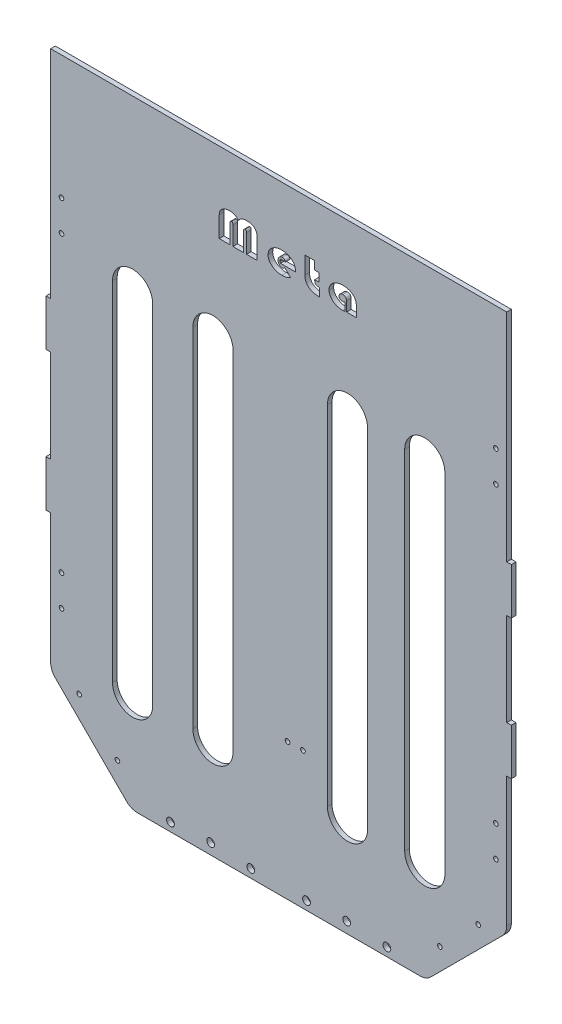
SolidWorks part; units mm, degrees
ref_plane "前视基准面" through (0, 0, 0) normal (0, 0, 1) x (1, 0, 0)
ref_plane "上视基准面" through (0, 0, 0) normal (0, 1, 0) x (1, 0, 0)
ref_plane "右视基准面" through (0, 0, 0) normal (1, 0, 0) x (0, 0, -1)
sketch "草图1" plane through (0, 0, 0) normal (0, 0, 1) x (1, 0, 0)
  line L0 (-147.5, 90) -> (-150.5, 90)
  line L1 (-147.5, 170) -> (147.5, 170)
  line L2 (-147.5, 170) -> (-147.5, 90)
  line L3 (-147.5, -170) -> (147.5, -170)
  line L4 (147.5, 170) -> (147.5, 90)
  line L5 (-147.5, 170) -> (147.5, -170) construction
  line L6 (-147.5, -170) -> (147.5, 170) construction
  line L7 (-150.5, 90) -> (-150.5, 60)
  line L8 (-150.5, 60) -> (-147.5, 60)
  line L9 (-147.5, 60) -> (-147.5, 0)
  line L10 (-147.5, 0) -> (-150.5, 0)
  line L11 (-150.5, 0) -> (-150.5, -30)
  line L12 (-150.5, -30) -> (-147.5, -30)
  line L13 (-147.5, -90) -> (-150.5, -90) construction
  line L14 (-150.5, -90) -> (-150.5, -120) construction
  line L15 (-150.5, -120) -> (-147.5, -120) construction
  line L16 (-147.5, -30) -> (-147.5, -90)
  line L17 (-147.5, -120) -> (-147.5, -170)
  line L18 (0, 0) -> (0, 121.9272) construction
  line L19 (147.5, -90) -> (150.5, -90) construction
  line L20 (150.5, -90) -> (150.5, -120) construction
  line L21 (150.5, -120) -> (147.5, -120) construction
  line L22 (147.5, 0) -> (150.5, 0)
  line L23 (150.5, 0) -> (150.5, -30)
  line L24 (150.5, -30) -> (147.5, -30)
  line L25 (147.5, 90) -> (150.5, 90)
  line L26 (150.5, 90) -> (150.5, 60)
  line L27 (150.5, 60) -> (147.5, 60)
  line L28 (147.5, -120) -> (147.5, -170)
  line L29 (147.5, -30) -> (147.5, -90)
  line L30 (147.5, 60) -> (147.5, 0)
  line L31 (-147.5, -90) -> (-147.5, -120)
  line L32 (147.5, -90) -> (147.5, -120)
  point P0 (0, 0)
  dimension "D1" = 295
  dimension "D2" = 340
  dimension "D3" = 30
  dimension "D4" = 3
  dimension "D5" = 80
  dimension "D6" = 3
  dimension "D7" = 30
  dimension "D8" = 30
  dimension "D9" = 3
  dimension "D10" = 50
  dimension "D11" = 60
extrude "凸台-拉伸1" add sketch "草图1" along normal blind 3
sketch "草图3" plane through (0, 0, 3) normal (0, 0, 1) x (1, 0, 0)
  line L0 (-147.5, -118) -> (-95.5, -170)
  line L1 (-147.5, -30) -> (-147.5, -170) construction
  line L2 (-147.5, -170) -> (147.5, -170) construction
  line L3 (-95.5, -170) -> (-147.5, -170)
  line L4 (-147.5, -170) -> (-147.5, -118)
  line L5 (147.5, -170) -> (147.5, -118)
  line L6 (147.5, -170) -> (147.5, -30) construction
  line L7 (147.5, -118) -> (95.5, -170)
  line L8 (95.5, -170) -> (147.5, -170)
  dimension "D1" = 52
  dimension "D2" = 52
  dimension "D3" = 52
  dimension "D4" = 52
extrude "切除-拉伸2" cut sketch "草图3" against normal through all
fillet "圆角1" [suppressed] radius 5
sketch "草图4" plane through (0, 0, 3) normal (0, 0, 1) x (1, 0, 0)
  line L0 (147.5, 170) -> (-147.5, 170) construction
  line L1 (147.5, 90) -> (147.5, 170) construction
  line L2 (147.5, -118) -> (147.5, -30) construction
  line L3 (0, 170) -> (0, 113.7599) construction
  circle A0 centre (140.5, 150) radius 1.5
  circle A1 centre (140.5, 130) radius 1.5
  circle A2 centre (140.5, -60) radius 1.5
  circle A3 centre (140.5, -80) radius 1.5
  circle A4 centre (-140.5, -80) radius 1.5
  circle A5 centre (-140.5, -60) radius 1.5
  circle A6 centre (-140.5, 130) radius 1.5
  circle A7 centre (-140.5, 150) radius 1.5
  dimension "D1" = 20
  dimension "D2" = 20
  dimension "D3" = 190
  dimension "D4" = 20
  dimension "D5" = 7
  dimension "D6" = 7
  dimension "D7" = 7
  dimension "D8" = 7
  dimension "D9" = 3
  dimension "D10" = 3
  dimension "D11" = 3
  dimension "D12" = 3
extrude "切除-拉伸3" cut sketch "草图4" against normal through all
sketch "草图5" plane through (0, 0, 3) normal (0, 0, 1) x (1, 0, 0)
  line L0 (-94.5, 120) -> (-94.5, -105) construction
  line L1 (-81.5, 120) -> (-81.5, -105)
  line L2 (-107.5, 120) -> (-107.5, -105)
  line L3 (147.5, 170) -> (-147.5, 170) construction
  line L4 (-147.5, 60) -> (-147.5, 0) construction
  line L5 (-42.5, 120) -> (-42.5, -105) construction
  line L6 (-29.5, 120) -> (-29.5, -105)
  line L7 (-55.5, 120) -> (-55.5, -105)
  line L8 (44.5, 120) -> (44.5, -105) construction
  line L9 (57.5, 120) -> (57.5, -105)
  line L10 (31.5, 120) -> (31.5, -105)
  line L11 (94.5, 120) -> (94.5, -105) construction
  line L12 (107.5, 120) -> (107.5, -105)
  line L13 (81.5, 120) -> (81.5, -105)
  arc A0 (-81.5, 120) -> (-107.5, 120) centre (-94.5, 120) ccw
  arc A1 (-107.5, -105) -> (-81.5, -105) centre (-94.5, -105) ccw
  arc A2 (-29.5, 120) -> (-55.5, 120) centre (-42.5, 120) ccw
  arc A3 (-55.5, -105) -> (-29.5, -105) centre (-42.5, -105) ccw
  arc A4 (57.5, 120) -> (31.5, 120) centre (44.5, 120) ccw
  arc A5 (31.5, -105) -> (57.5, -105) centre (44.5, -105) ccw
  arc A6 (107.5, 120) -> (81.5, 120) centre (94.5, 120) ccw
  arc A7 (81.5, -105) -> (107.5, -105) centre (94.5, -105) ccw
  point P2 (-94.5, 7.5)
  point P14 (-42.5, 7.5)
  point P22 (44.5, 7.5)
  point P29 (94.5, 7.5)
  dimension "D1" = 13
  dimension "D2" = 225
  dimension "D3" = 50
  dimension "D4" = 53
  dimension "D8" = 52
  dimension "D9" = 87
  dimension "D5" = 2
  dimension "D6" = 2
  dimension "D7" = 2
extrude "切除-拉伸4" cut sketch "草图5" against normal through all
fillet "圆角3" radius 10 4 edges at (147.5, -118, 1.5) (95.5, -170, 1.5) (-95.5, -170, 1.5) (-147.5, -118, 1.5)
sketch "草图8" plane through (0, 0, 3) normal (0, 0, 1) x (1, 0, 0)
  line L0 (-129.0441, -122.3138) -> (-104.2954, -147.0625) construction
  line L1 (-98.4289, -167.0711) -> (-144.5711, -120.9289) construction
  line L2 (-147.5, -99.7493) -> (147.5, -99.7493) construction
  line L3 (-147.5, -30) -> (-147.5, -113.8579) construction
  line L4 (147.5, -113.8579) -> (147.5, -30) construction
  line L5 (0, -99.7493) -> (0, -54.3911) construction
  line L6 (129.0441, -122.3138) -> (104.2954, -147.0625) construction
  circle A0 centre (-129.0441, -122.3138) radius 1.5
  circle A1 centre (-104.2954, -147.0625) radius 1.5
  circle A2 centre (104.2954, -147.0625) radius 1.5
  circle A3 centre (129.0441, -122.3138) radius 1.5
  dimension "D1" = 3
  dimension "D2" = 3
  dimension "D3" = 10
  dimension "D4" = 35
extrude "切除-拉伸5" cut sketch "草图8" against normal through all
sketch "草图9" plane through (0, 0, 3) normal (0, 0, 1) x (1, 0, 0)
  line L1 (147.5, 170) -> (-147.5, 170)
  line L2 (147.5, 170) -> (147.5, 230)
  line L3 (147.5, 230) -> (-147.5, 230)
  line L4 (-147.5, 170) -> (-147.5, 230)
  dimension "D1" = 60
extrude "凸台-拉伸2" add sketch "草图9" against normal blind 3
sketch "草图10" plane through (0, 0, 0) normal (0, 0, -1) x (-1, 0, 0)
  circle A0 centre (-15.7145, -81.4977) radius 1.5
  circle A1 centre (-5.7145, -81.4977) radius 1.5
extrude "切除-拉伸6" cut sketch "草图10" against normal blind 10
sketch "草图12" plane through (0, 0, 3) normal (0, 0, 1) x (1, 0, 0)
  text T0 "Meta\r\n" font "宋体" height in points 72
extrude "切除-拉伸7" cut sketch "草图12" against normal blind 10
sketch "草图13" plane through (0, 0, 3) normal (0, 0, 1) x (1, 0, 0)
  line L0 (0, -37.6582) -> (0, -192.8591) construction
  line L1 (-91.3579, -170) -> (91.3579, -170) construction
  line L2 (-18, -164.5) -> (-70, -164.5) construction
  line L3 (-44, -164.5) -> (-44, -139.879) construction
  circle A0 centre (-18, -164.5) radius 2.5
  circle A1 centre (-70, -164.5) radius 2.5
  circle A2 centre (-44, -163) radius 2.5
  circle A3 centre (70, -164.5) radius 2.5
  circle A4 centre (44, -163) radius 2.5
  circle A5 centre (18, -164.5) radius 2.5
  dimension "D1" = 5.5
  dimension "D2" = 52
  dimension "D3" = 7
  dimension "D4" = 18
extrude "切除-拉伸8" cut sketch "草图13" against normal blind 10
